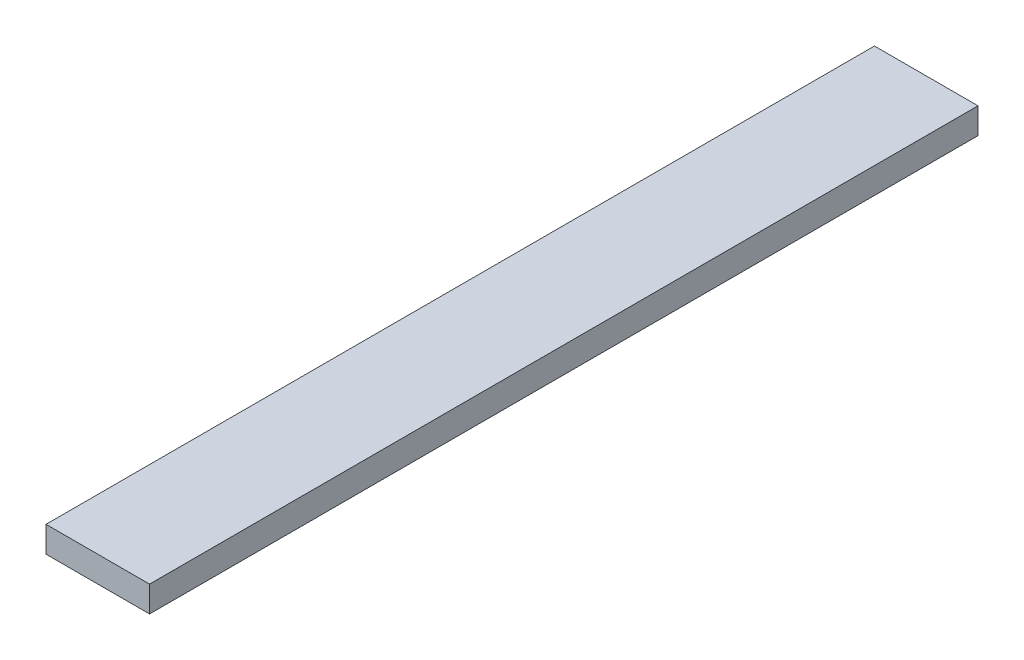
SolidWorks part; units mm, degrees
material "Pine"
ref_plane "Front Plane" through (0, 0, 0) normal (0, 0, 1) x (1, 0, 0)
ref_plane "Top Plane" through (0, 0, 0) normal (0, 1, 0) x (1, 0, 0)
ref_plane "Right Plane" through (0, 0, 0) normal (1, 0, 0) x (0, 0, -1)
sketch "Sketch1" plane through (0, 0, 0) normal (0, 1, 0) x (1, 0, 0)
  line L1 (-38.1, 304.8) -> (38.1, 304.8)
  line L2 (-38.1, 304.8) -> (-38.1, -304.8)
  line L3 (-38.1, -304.8) -> (38.1, -304.8)
  line L4 (38.1, 304.8) -> (38.1, -304.8)
  line L5 (-38.1, 304.8) -> (38.1, -304.8) construction
  line L6 (-38.1, -304.8) -> (38.1, 304.8) construction
  point P0 (0, 0)
  dimension "D1" = 609.6
  dimension "D2" = 76.2
extrude "Boss-Extrude1" add sketch "Sketch1" along normal blind 19.05
